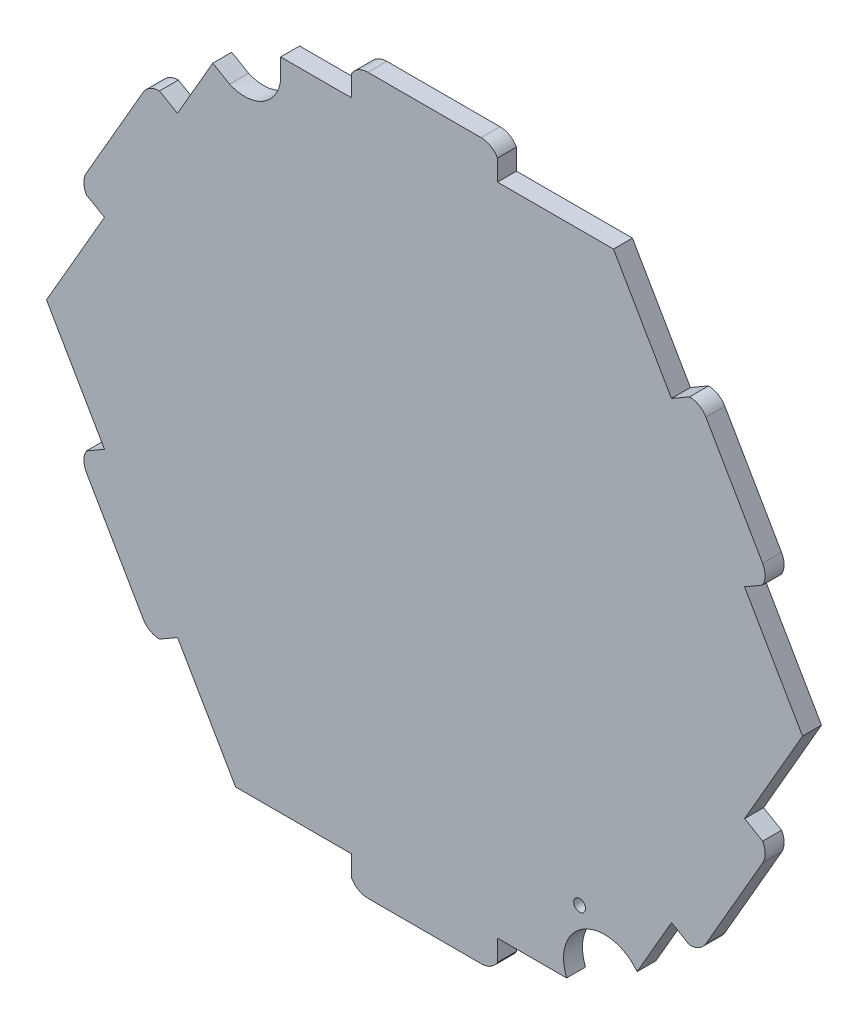
SolidWorks part; units mm, degrees
ref_plane "Alzado" through (0, 0, 0) normal (0, 0, 1) x (1, 0, 0)
ref_plane "Planta" through (0, 0, 0) normal (0, 1, 0) x (1, 0, 0)
ref_plane "Vista lateral" through (0, 0, 0) normal (1, 0, 0) x (0, 0, -1)
sketch "Croquis1" plane through (0, 0, 0) normal (0, 0, 1) x (1, 0, 0)
  line L0 (-19.2969, 91.8991) -> (-19.2969, 86.3943)
  line L1 (49.8642, 86.4085) -> (19.2613, 86.4022)
  line L2 (-55.8866, 76.0137) -> (-65.1959, 59.8819)
  line L3 (-99.7641, -0.0205) -> (-84.4571, -26.5203)
  line L4 (-49.8642, -86.4085) -> (-19.2613, -86.4022)
  line L5 (56.0945, -75.6534) -> (65.1959, -59.8819)
  line L6 (99.7641, 0.0205) -> (84.4571, 26.5203)
  line L7 (-14.9673, 94.3982) -> (14.9317, 94.3982)
  line L8 (19.2613, 91.8991) -> (19.2613, 86.4022)
  line L10 (89.2176, 29.2688) -> (84.4571, 26.5203)
  line L11 (74.2676, 60.1611) -> (89.2171, 34.2679)
  line L12 (69.9385, 62.6611) -> (65.1712, 59.9087)
  line L13 (69.9563, -62.6303) -> (65.1959, -59.8819)
  line L14 (89.2349, -34.2371) -> (74.2854, -60.1303)
  line L15 (89.2354, -29.238) -> (84.4681, -26.4856)
  line L16 (-19.2613, -91.8991) -> (-19.2613, -86.4022)
  line L17 (14.9673, -94.3982) -> (-14.9317, -94.3982)
  line L18 (19.2969, -91.8991) -> (19.2969, -86.3943)
  line L19 (-89.2176, -29.2688) -> (-84.4571, -26.5203)
  line L20 (-74.2676, -60.1611) -> (-89.2171, -34.2679)
  line L21 (-69.9385, -62.6611) -> (-65.1712, -59.9087)
  line L22 (-69.9563, 62.6303) -> (-65.1959, 59.8819)
  line L23 (-89.2349, 34.2371) -> (-74.2854, 60.1303)
  line L24 (-89.2354, 29.238) -> (-84.4681, 26.4856)
  line L25 (-84.4681, 26.4856) -> (-99.7641, -0.0205)
  line L26 (-65.1712, -59.9087) -> (-49.8642, -86.4085)
  line L27 (19.2969, -86.3943) -> (37.4956, -86.3905)
  line L28 (84.4681, -26.4856) -> (99.7641, 0.0205)
  line L29 (65.1712, 59.9087) -> (49.8642, 86.4085)
  line L34 (-19.2969, 86.3943) -> (-37.9679, 86.3943)
  line L35 (-37.9679, 86.3943) -> (-37.9679, 81.1201)
  line L38 (-55.8867, 76.0137) -> (-51.4157, 73.4333)
  circle A0 centre (0, 0) radius 86.3982 construction
  arc A1 (14.9317, 94.3982) -> (19.2613, 91.8991) centre (14.9317, 89.3982) cw
  arc A2 (-19.2969, 91.8991) -> (-14.9673, 94.3982) centre (-14.9673, 89.3982) cw
  arc A3 (89.2171, 34.2679) -> (89.2176, 29.2688) centre (84.887, 31.7679) cw
  arc A4 (69.9385, 62.6611) -> (74.2676, 60.1611) centre (69.9375, 57.6611) cw
  arc A5 (74.2854, -60.1303) -> (69.9563, -62.6303) centre (69.9553, -57.6303) cw
  arc A6 (89.2354, -29.238) -> (89.2349, -34.2371) centre (84.9048, -31.7371) cw
  arc A7 (-14.9317, -94.3982) -> (-19.2613, -91.8991) centre (-14.9317, -89.3982) cw
  arc A8 (19.2969, -91.8991) -> (14.9673, -94.3982) centre (14.9673, -89.3982) cw
  arc A9 (-89.2171, -34.2679) -> (-89.2176, -29.2688) centre (-84.887, -31.7679) cw
  arc A10 (-69.9385, -62.6611) -> (-74.2676, -60.1611) centre (-69.9375, -57.6611) cw
  arc A11 (-74.2854, 60.1303) -> (-69.9563, 62.6303) centre (-69.9553, 57.6303) cw
  arc A12 (-89.2354, 29.238) -> (-89.2349, 34.2371) centre (-84.9048, 31.7371) cw
  arc A14 (56.0945, -75.6534) -> (37.4956, -86.3905) centre (47.5127, -82.2651) ccw
  arc A19 (-51.4157, 73.4333) -> (-37.9679, 81.1201) centre (-47.5102, 82.2075) ccw
  point P60 (0, 0)
  dimension "D1" = 5
  dimension "D2" = 6
extrude "Saliente-Extruir1" add sketch "Croquis1" along normal blind 5 contours A19 L38 L2 L22 A11 L23 A12 L24 L25 L3 L19 A9 L20 A10 L21 L26 L4 L16 A7 L17 A8 L18 L27 A14 L5 L13 A5 L14 A6 L15 L28 L6 L10 A3 L11 A4 L12 L29 L1 L8 A1 L7 A2 L0 L34 L35
sketch "Croquis2" plane through (0, 0, 5) normal (0, 0, 1) x (1, 0, 0)
  circle A0 centre (40.9347, -68.0582) radius 1.5631
extrude "Cortar-Extruir1" cut sketch "Croquis2" against normal blind 10
